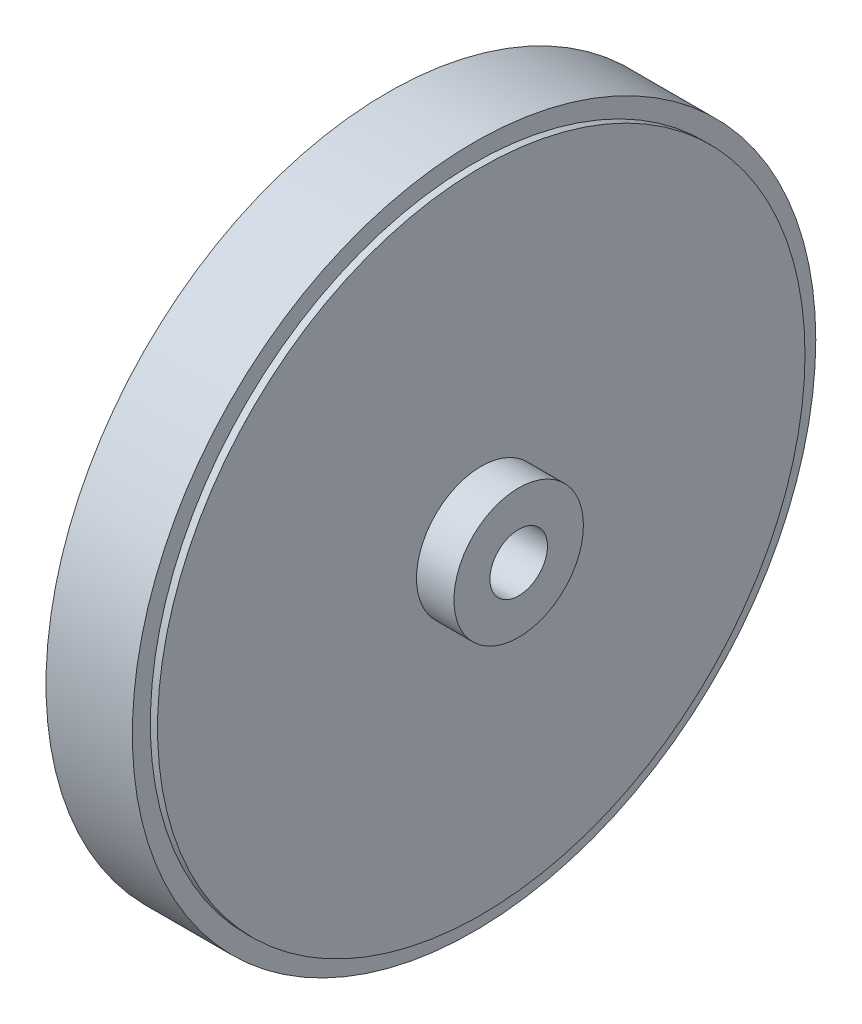
SolidWorks part; units mm, degrees
ref_plane "前视基准面" through (0, 0, 0) normal (0, 0, 1) x (1, 0, 0)
ref_plane "上视基准面" through (0, 0, 0) normal (0, 1, 0) x (1, 0, 0)
ref_plane "右视基准面" through (0, 0, 0) normal (1, 0, 0) x (0, 0, -1)
sketch "草图2" plane through (0, 0, 0) normal (1, 0, 0) x (0, 0, -1)
  circle A0 centre (0, 0) radius 47.5
  circle A1 centre (0, 0) radius 4
  dimension "D1" = 95
extrude "凸台-拉伸1" add sketch "草图2" along normal blind 12
sketch "草图3" plane through (12, 0, 0) normal (1, 0, 0) x (0, 0, -1)
  circle A0 centre (0, 0) radius 45
  circle A1 centre (0, 0) radius 4
  dimension "D1" = 90
  dimension "D2" = 8
extrude "凸台-拉伸2" add sketch "草图3" along normal blind 1 and the other way blind 13
sketch "草图4" plane through (13, 0, 0) normal (1, 0, 0) x (0, 0, -1)
  circle A0 centre (0, 0) radius 9
  circle A1 centre (0, 0) radius 4
  dimension "D1" = 18
  dimension "D2" = 8
extrude "凸台-拉伸3" add sketch "草图4" along normal blind 5.2
